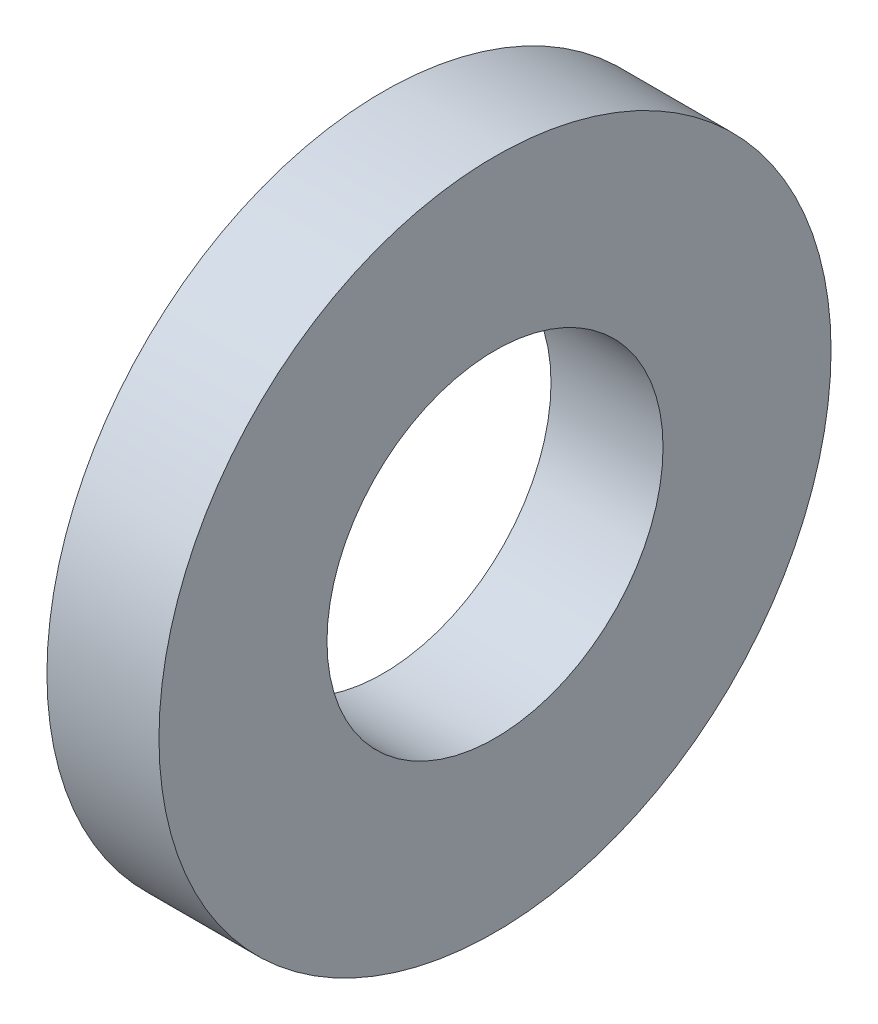
SolidWorks part; units mm, degrees
material "Plain Carbon Steel"
ref_plane "Front Plane" through (0, 0, 0) normal (0, 0, 1) x (1, 0, 0)
ref_plane "Top Plane" through (0, 0, 0) normal (0, 1, 0) x (1, 0, 0)
ref_plane "Right Plane" through (0, 0, 0) normal (1, 0, 0) x (0, 0, -1)
sketch "Sketch1" plane through (0, 0, 0) normal (0, 0, 1) x (1, 0, 0)
  line L0 (0, 0) -> (26.4176, 0) construction
  line L2 (0, 3) -> (1, 3)
  line L3 (0, 3) -> (0, 1.5)
  line L4 (0, 1.5) -> (1, 1.5)
  line L5 (1, 3) -> (1, 1.5)
  dimension "D1" = 3
  dimension "D2" = 6
  dimension "D3" = 1
revolve "Revolve1" add sketch "Sketch1" angle 360 about L0
